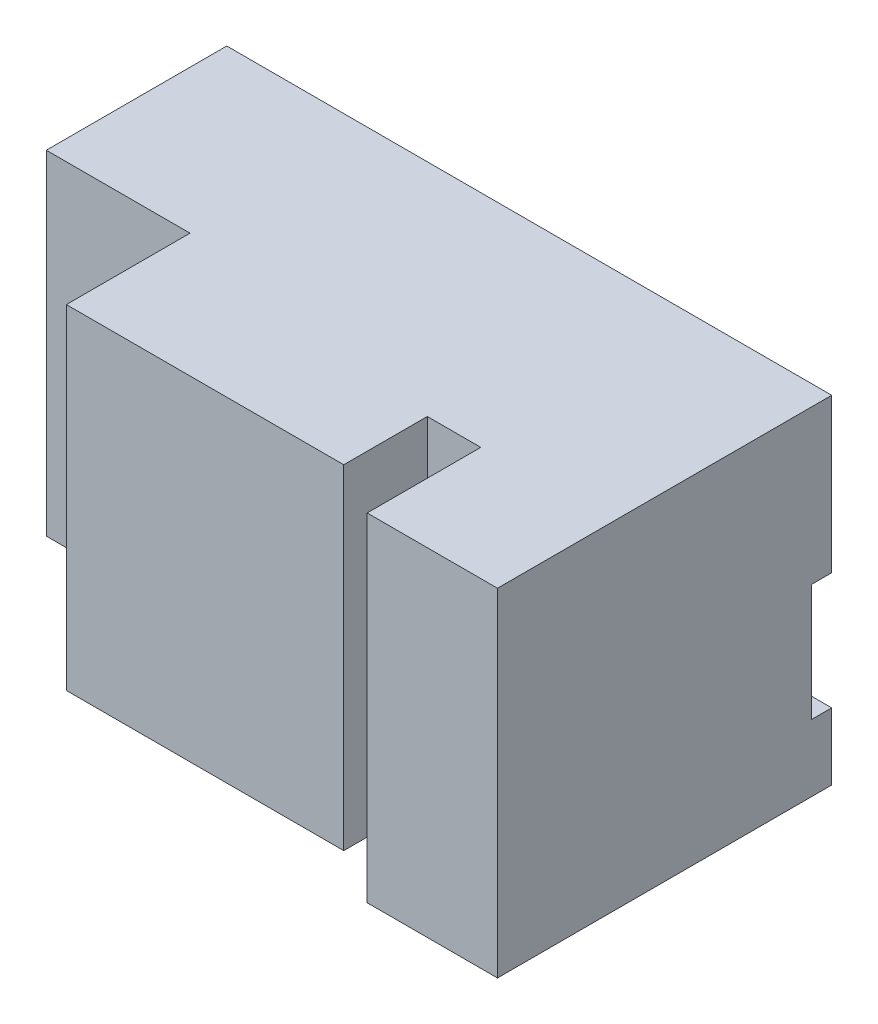
SolidWorks part; units mm, degrees
ref_plane "Front Plane" through (0, 0, 0) normal (0, 0, 1) x (1, 0, 0)
ref_plane "Top Plane" through (0, 0, 0) normal (0, 1, 0) x (1, 0, 0)
ref_plane "Right Plane" through (0, 0, 0) normal (1, 0, 0) x (0, 0, -1)
sketch "Sketch2" plane through (0, 0, 0) normal (0, 0, 1) x (1, 0, 0)
  line L1 (-21.5, -50) -> (21.5, -50)
  line L2 (-21.5, -50) -> (-21.5, 50)
  line L3 (-21.5, 50) -> (21.5, 50)
  line L4 (21.5, -50) -> (21.5, 50)
  line L5 (-21.5, -50) -> (21.5, 50) construction
  line L6 (-21.5, 50) -> (21.5, -50) construction
  point P0 (0, 0)
  dimension "D1" = 43
  dimension "D2" = 100
extrude "Boss-Extrude1" add sketch "Sketch2" along normal blind 54
sketch "Sketch3" plane through (0, 0, 0) normal (0, 0, 1) x (1, 0, 0)
  line L0 (-21.5, -50) -> (21.5, -50) construction
  line L1 (21.5, 50) -> (104.5, 50)
  line L2 (21.5, 50) -> (21.5, -50)
  line L3 (21.5, -50) -> (104.5, -50)
  line L4 (104.5, 50) -> (104.5, -50)
  dimension "D1" = 83
extrude "Boss-Extrude2" add sketch "Sketch3" along normal blind 91
sketch "Sketch4" plane through (0, 0, 0) normal (0, 0, 1) x (1, 0, 0)
  line L0 (21.5, -50) -> (104.5, -50) construction
  line L1 (104.5, 50) -> (120.5, 50)
  line L2 (104.5, 50) -> (104.5, -50)
  line L3 (104.5, -50) -> (120.5, -50)
  line L4 (120.5, 50) -> (120.5, -50)
  dimension "D1" = 16
extrude "Boss-Extrude3" add sketch "Sketch4" along normal blind 66
sketch "Sketch6" plane through (0, 0, 0) normal (0, 0, 1) x (1, 0, 0)
  line L0 (104.5, -50) -> (120.5, -50) construction
  line L1 (120.5, 50) -> (159.5, 50)
  line L2 (120.5, 50) -> (120.5, -50)
  line L3 (120.5, -50) -> (159.5, -50)
  line L4 (159.5, 50) -> (159.5, -50)
  dimension "D1" = 39
extrude "Boss-Extrude4" add sketch "Sketch6" along normal blind 100
sketch "Sketch5" plane through (159.5, 0, 0) normal (1, 0, 0) x (0, 0, -1)
  line L3 (0, -31) -> (-6, -31)
  line L4 (-6, 4) -> (-6, -31)
  line L6 (-100, -50) -> (0, -50) construction
  line L7 (-6, 4) -> (0, 4)
  line L8 (0, 55) -> (0, -55) construction
  line L9 (0, 4) -> (0, -31)
  dimension "D1" = 6
  dimension "D2" = 35
  dimension "D3" = 19
extrude "Cut-Extrude1" cut sketch "Sketch5" against normal blind 200
sketch "Sketch7" plane through (0, -50, 0) normal (0, -1, 0) x (1, 0, 0)
  line L0 (120.5, 100) -> (120.5, 0)
  line L1 (-21.5, 0) -> (159.5, 0) construction
  line L2 (159.5, 0) -> (120.5, 0)
  line L3 (159.5, 0) -> (159.5, 100)
  line L4 (159.5, 100) -> (120.5, 100)
extrude "Boss-Extrude5" add sketch "Sketch7" along normal blind 1
